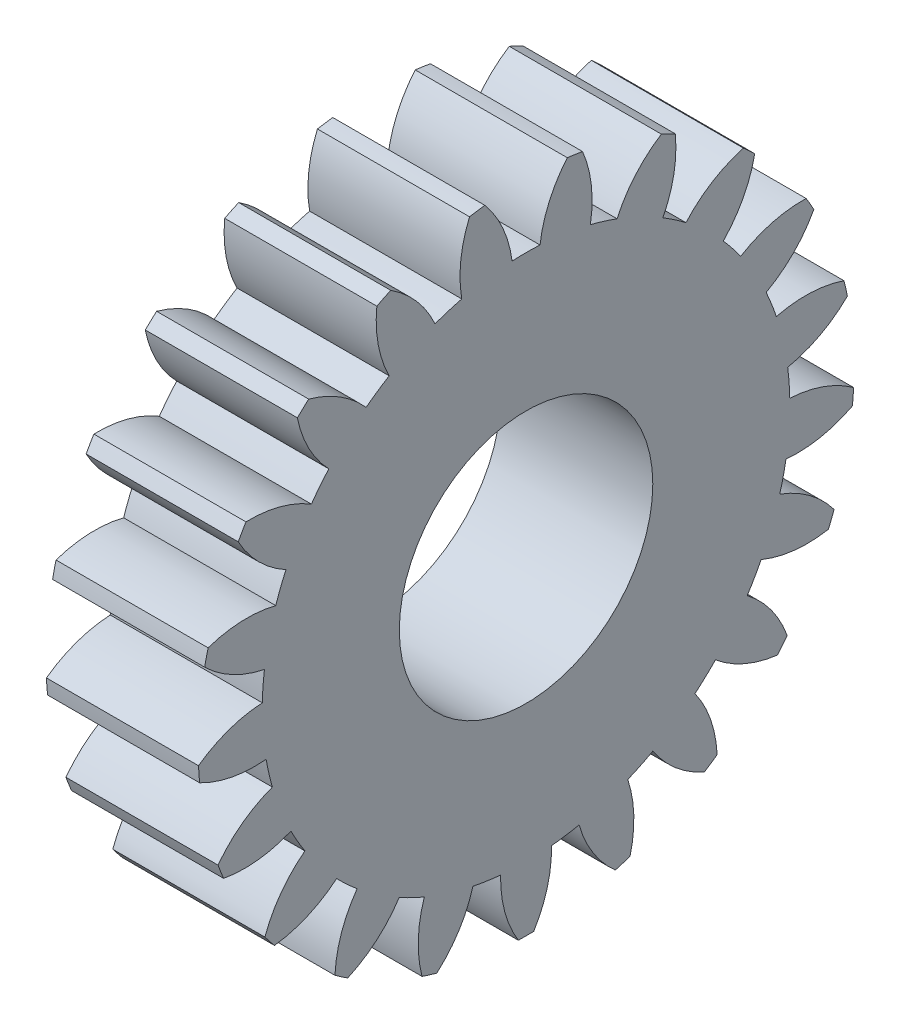
SolidWorks part; units mm, degrees
ref_plane "Plane1" through (0, 0, 0) normal (0, 0, 1) x (1, 0, 0)
ref_plane "Plane2" through (0, 0, 0) normal (0, 1, 0) x (1, 0, 0)
ref_plane "Plane3" through (0, 0, 0) normal (1, 0, 0) x (0, 0, -1)
sketch "HoldingSke" plane through (0, 0, 0) normal (0, 1, 0) x (1, 0, 0)
  line L0 (0, 0) -> (0.4149, -0.1593)
  line L1 (-15, 0) -> (100, 0) construction
  line L2 (0, 0) -> (-2.1039, 2.3779)
  line L3 (0, 0) -> (-11.863, 4.5341)
  line L4 (0, 0) -> (8.0624, 3.0949)
  line L5 (0, 0) -> (-46.8476, -17.4728)
  line L6 (0, 0) -> (-9.9476, -6.7116)
  line L7 (-2.1039, 2.3779) -> (8.6586, 51.2059)
  line L8 (-76.2, 54.61) -> (-73.4, 54.61)
  line L9 (-71.009, 38.7566) -> (-53.1078, 45.2721)
  line L10 (-76.2, 71.12) -> (104.1128, 71.12)
  line L11 (0, 0) -> (-12, 0)
  line L12 (-76.2, 101.6) -> (-76.123, 101.6)
  line L13 (24.9733, 27.94) -> (52.9518, 28.4284)
  line L14 (24.9733, 27.94) -> (24.9743, 27.94)
  line L15 (24.9733, 27.94) -> (100.4006, 29.5858)
  line L16 (-63.627, -2.25) -> (-12.827, -2.25)
  circle A0 centre (0, 0) radius 10
  circle A1 centre (0, 0) radius 20.8115
  circle A2 centre (0, 0) radius 37.5
  circle A3 centre (0, 0) radius 10
  dimension "MHD" = 41.623
  dimension "Hub_dia" = 75
  dimension "Bore" = 20
  dimension "MBD" = 20
  dimension "Num_teeth" = 21
  dimension "Pitch" = 0.4444
  dimension "Overall_len" = 50
  dimension "Show_teeth" = 21
  dimension "Thickness" = 12
  dimension "OAL" = 50.0001
  dimension "T_dim" = 2.8
  dimension "Ap" = 20
  dimension "H" = 19.05
  dimension "Pitch_radius" = 180.3128
  dimension "Width" = 12
  dimension "Backlash" = 0.077
  dimension "Addendum_fac" = 1
  dimension "Dedendum_fac" = 1.25
  dimension "Clearance_fac" = 0.25
  dimension "Dedendum_add" = 0.001
  dimension "Module" = 2.25
sketch "BasProSke" plane through (0, 0, 0) normal (0, 1, 0) x (1, 0, 0)
  line L0 (-10, 0) -> (60, 0) construction
  line L1 (0, 0) -> (0, 25.875)
  line L2 (0, 0) -> (12, 0)
  line L3 (12, 0) -> (12, 25.875)
  line L4 (12, 25.875) -> (0, 25.875)
  dimension "Thickness" = 12
  dimension "Diameter" = 51.75
revolve "Base-Revolve" add sketch "BasProSke" angle 360 about L0
sketch "TooCutSke" plane through (0, 0, 0) normal (1, 0, 0) x (0, 0, -1)
  line L1 (0, 0) -> (0, 107) construction
  line L2 (0, 0) -> (-1.9002, 23.5485) construction
  line L3 (0, 0) -> (-7.0255, 46.6108) construction
  line L4 (-1.9002, 23.5485) -> (-3.5127, 23.3054) construction
  arc A0 (1.1014, 20.7823) -> (-1.1014, 20.7823) centre (0, 0) ccw
  arc A1 (3.2722, 25.6929) -> (-3.2722, 25.6929) centre (0, 0) ccw
  circle A2 centre (0, 0) radius 23.625 construction
  circle A3 centre (0, 0) radius 22.2002 construction
  arc A4 (-1.1014, 20.7823) -> (-3.2722, 25.6929) centre (-10.4739, 19.5742) ccw
  arc A5 (3.2722, 25.6929) -> (1.1014, 20.7823) centre (10.4739, 19.5742) ccw
  dimension "Root_dia" = 41.623
  dimension "Overcut_dia" = 51.8008
  dimension "Pitch_dia" = 47.25
  dimension "Base_dia" = 44.4005
  dimension "Flank_rad" = 9.45
  dimension "Half_ang" = 8.571
  dimension "Half_CT" = 1.6307
extrude "ToothCut" cut sketch "TooCutSke" along normal through all
fillet "Breaks" [suppressed] radius 0.045
fillet "RootFillets" [suppressed] radius 0.5635
pattern_circular "TeethCuts" count 21 every 17.143 about axis through (-10, 0, 0) along (1, 0, 0) of "ToothCut", "RootFillets", "Breaks"
sketch "HubNeaOneSke" plane through (0, 0, 0) normal (-1, 0, 0) x (0, 0, 1)
  circle A0 centre (0, 0) radius 20.8115
  dimension "Diameter" = 41.623
extrude "HubNearOne" [suppressed] add sketch "HubNeaOneSke" along normal blind 38.0001
sketch "HubNeaBotSke" plane through (0, 0, 0) normal (-1, 0, 0) x (0, 0, 1)
  circle A0 centre (0, 0) radius 20.8115
  dimension "Diameter" = 41.623
extrude "HubNearBoth" [suppressed] add sketch "HubNeaBotSke" along normal blind 19
ref_plane "FarPln" through (12, 0, 0) normal (1, 0, 0) x (0, 0, -1)
sketch "HubFarSke" plane through (12, 0, 0) normal (1, 0, 0) x (0, 0, -1)
  circle A0 centre (0, 0) radius 20.8115
  dimension "Diameter" = 41.623
extrude "HubFar" [suppressed] add sketch "HubFarSke" along normal blind 19
sketch "BorSke" plane through (0, 0, 0) normal (1, 0, 0) x (0, 0, -1)
  circle A0 centre (0, 0) radius 10
  dimension "Diameter" = 20
extrude "Bore" cut sketch "BorSke" along normal mid plane 100.0001
sketch "KeySke" plane through (0, 0, 0) normal (1, 0, 0) x (0, 0, -1)
  line L0 (-3, 0) -> (-3, 12.8)
  line L1 (-3, 12.8) -> (3, 12.8)
  line L2 (3, 12.8) -> (3, 0)
  line L3 (0, 0) -> (0, 34) construction
  line L4 (-3, 0) -> (3, 0)
  dimension "Offset" = 12.8
  dimension "Width" = 6
extrude "Keyway" [suppressed] cut sketch "KeySke" along normal mid plane 100.0001
pattern_circular "Keyway2" [suppressed] count 2 every 90 about axis through (-10, 0, 0) along (1, 0, 0)
equation "' \"Module@HoldingSke\" = 6.35"
equation "' \"Num_teeth@HoldingSke\" = 12"
equation "' \"Ap@HoldingSke\" =  20"
equation "' \"Ap@HoldingSke\" = 20"
equation "' \"Width@HoldingSke\" = 0.5 * 25.4"
equation "' \"Hub_dia@HoldingSke\"= 1 * 25.4"
equation "' \"Hub_dia@HoldingSke\" = 1 * 25.4"
equation "' \"Overall_len@HoldingSke\" = 1.0 * 25.4"
equation "' \"Bore@HoldingSke\" = 0.75 * 25.4"
equation "' \"T_dim@HoldingSke\" = 0.1 * 25.4"
equation "' \"Width@KeySke\" = 0.25 * 25.4"
equation "' \"Show_teeth@HoldingSke\" = 13"
equation "' \"Backlash@HoldingSke\" = 0.009 * 25.4"
equation "' \"Addendum_fac@HoldingSke\" = 1.0"
equation "' \"Dedendum_fac@HoldingSke\" = 1.25"
equation "' \"Dedendum_add@HoldingSke\" = 0.00005 * 25.4"
equation "' \"Clearance_fac@HoldingSke\" = 0.25"
equation "\"Pitch@HoldingSke\" = 1 / \"Module@HoldingSke\""
equation "\"Overcut_dia@TooCutSke\" = (\"Num_teeth@HoldingSke\" + 2 * \"Addendum_fac@HoldingSke\") / \"Pitch@HoldingSke\" + 0.002 * 25.4"
equation "\"Pitch_dia@TooCutSke\" = \"Num_teeth@HoldingSke\" / \"Pitch@HoldingSke\""
equation "\"Base_dia@TooCutSke\" = \"Num_teeth@HoldingSke\" / \"Pitch@HoldingSke\" * cos((\"Ap@HoldingSke\"  * 3.14159265 / 180))"
equation "\"Root_dia@TooCutSke\" = (\"Num_teeth@HoldingSke\" + 2) / \"Pitch@HoldingSke\" - 2 * (\"Addendum_fac@HoldingSke\" + \"Dedendum_fac@HoldingSke\") / \"Pitch@HoldingSke\" - \"Dedendum_add@HoldingSke\" * 2"
equation "\"Half_ang@TooCutSke\" = 180 / \"Num_teeth@HoldingSke\""
equation "\"Half_CT@TooCutSke\" = \"Num_teeth@HoldingSke\" / \"Pitch@HoldingSke\" * sin((3.14159265 / 2 / \"Num_teeth@HoldingSke\")) / 2 - 7 * \"Backlash@HoldingSke\" / 4"
equation "\"Flank_rad@TooCutSke\" = \"Num_teeth@HoldingSke\" / \"Pitch@HoldingSke\" / 5"
equation "\"Radius@RootFillets\" = \"Clearance_fac@HoldingSke\" / \"Pitch@HoldingSke\" + \"Dedendum_add@HoldingSke\""
equation "\"Break_rad@Breaks\" = 0.02 / \"Pitch@HoldingSke\""
equation "\"Thickness@HoldingSke\" = \"Width@HoldingSke\""
equation "\"OAL@HoldingSke\" = \"Thickness@HoldingSke\""
equation "\"MHD@HoldingSke\" = (\"Num_teeth@HoldingSke\" + 2) / \"Pitch@HoldingSke\" - 2 * (\"Addendum_fac@HoldingSke\" + \"Dedendum_fac@HoldingSke\")  / \"Pitch@HoldingSke\" - \"Dedendum_add@HoldingSke\" * 2"
equation "\"MBD@HoldingSke\" = (\"Num_teeth@HoldingSke\" + 2) / \"Pitch@HoldingSke\" - 2 * (\"Addendum_fac@HoldingSke\" + \"Dedendum_fac@HoldingSke\")  / \"Pitch@HoldingSke\" - \"Dedendum_add@HoldingSke\" * 2 - 0.002 * 25.4"
equation "\"MHD@HoldingSke\" = ((sgn( \"MHD@HoldingSke\" - \"Hub_dia@HoldingSke\" )-1)*( \"MHD@HoldingSke\" - \"Hub_dia@HoldingSke\" ))/-2+ \"Hub_dia@HoldingSke\""
equation "\"MBD@HoldingSke\" = ((sgn( \"MBD@HoldingSke\" - \"Bore@HoldingSke\" )-1)*( \"MBD@HoldingSke\" - \"Bore@HoldingSke\" ))/-2+ \"Bore@HoldingSke\""
equation "\"OAL@HoldingSke\" = ((sgn( \"OAL@HoldingSke\" - \"Overall_len@HoldingSke\" )+1)*( \"OAL@HoldingSke\" - \"Overall_len@HoldingSke\" ))/2 + \"Overall_len@HoldingSke\" + 0.000002 * 25.4"
equation "\"Num_teeth@TeethCuts\" = int( \"Show_teeth@HoldingSke\" ) + 1"
equation "\"Num_teeth@TeethCuts\" = ((sgn( \"Num_teeth@TeethCuts\" - \"Num_teeth@HoldingSke\" )-1)*( \"Num_teeth@TeethCuts\" - \"Num_teeth@HoldingSke\" ))/-2+ \"Num_teeth@HoldingSke\""
equation "\"Num_teeth@TeethCuts\" = ((sgn( \"Num_teeth@TeethCuts\" - 2.0)+1)*( \"Num_teeth@TeethCuts\" - 2.0))/2 +2.0"
equation "\"Angle@TeethCuts\" = 360.0 / \"Num_teeth@HoldingSke\""
equation "\"Diameter@BasProSke\" = (\"Num_teeth@HoldingSke\" + 2 * \"Addendum_fac@HoldingSke\") / \"Pitch@HoldingSke\""
equation "\"Thickness@BasProSke\"  = \"Thickness@HoldingSke\""
equation "' \"Fillet_rad@BasProSke\" =  \"Thickness@HoldingSke\" * 0.05"
equation "' \"Fillet_rad@BasProSke\" = \"Thickness@HoldingSke\" * 0.05"
equation "\"MHD@HoldingSke\" = ((sgn( \"MHD@HoldingSke\" - \"Root_dia@TooCutSke\" )-1)*( \"MHD@HoldingSke\" - \"Root_dia@TooCutSke\" ))/-2+ \"Root_dia@TooCutSke\""
equation "\"Diameter@HubNeaOneSke\" = \"MHD@HoldingSke\""
equation "\"Length@HubNearOne\" = \"OAL@HoldingSke\" - \"Thickness@BasProSke\""
equation "\"Diameter@HubNeaBotSke\" = \"MHD@HoldingSke\""
equation "\"Length@HubNearBoth\" = ( \"OAL@HoldingSke\" - \"Thickness@BasProSke\" ) / 2.0"
equation "\"Thickness@FarPln\" = \"Thickness@BasProSke\""
equation "\"Diameter@HubFarSke\" = \"MHD@HoldingSke\""
equation "\"Length@HubFar\" = ( \"OAL@HoldingSke\" - \"Thickness@BasProSke\" ) / 2.0"
equation "\"Diameter@BorSke\" = \"MBD@HoldingSke\""
equation "\"D1@Bore\" = \"OAL@HoldingSke\" * 2.0"
equation "\"D1@Keyway\" = \"OAL@HoldingSke\" * 2.0"
equation "\"Offset@KeySke\" = \"T_dim@HoldingSke\" + \"MBD@HoldingSke\" / 2.0"
